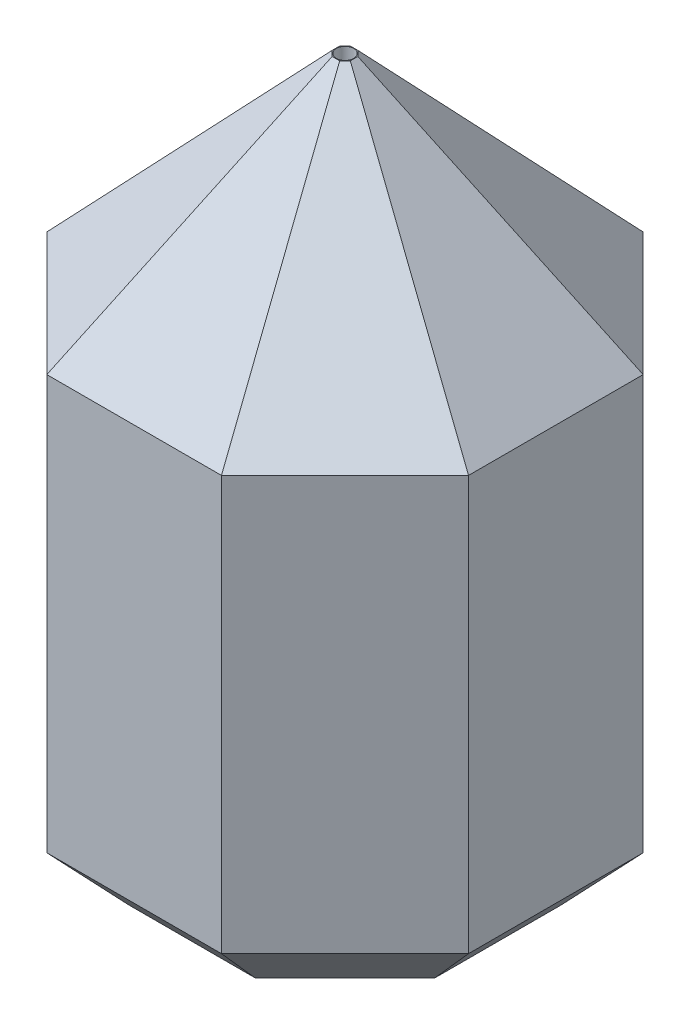
SolidWorks part; units mm, degrees
ref_plane "Front Plane" through (0, 0, 0) normal (0, 0, 1) x (1, 0, 0)
ref_plane "Top Plane" through (0, 0, 0) normal (0, 1, 0) x (1, 0, 0)
ref_plane "Right Plane" through (0, 0, 0) normal (1, 0, 0) x (0, 0, -1)
sketch "Sketch1" plane through (0, 0, 0) normal (0, 1, 0) x (1, 0, 0)
  line L1 (-17, -17) -> (17, -17)
  line L2 (-17, -17) -> (-17, 17)
  line L3 (-17, 17) -> (17, 17)
  line L4 (17, -17) -> (17, 17)
  line L5 (-17, -17) -> (17, 17) construction
  line L6 (-17, 17) -> (17, -17) construction
  line L7 (-15.136, 36.5416) -> (-36.5416, 15.136)
  line L8 (-36.5416, 15.136) -> (-36.5416, -15.136)
  line L9 (-36.5416, -15.136) -> (-15.136, -36.5416)
  line L10 (-15.136, -36.5416) -> (15.136, -36.5416)
  line L11 (15.136, -36.5416) -> (36.5416, -15.136)
  line L12 (36.5416, -15.136) -> (36.5416, 15.136)
  line L13 (36.5416, 15.136) -> (15.136, 36.5416)
  line L14 (15.136, 36.5416) -> (-15.136, 36.5416)
  circle A0 centre (0, 0) radius 36.5416 construction
  point P0 (0, 0)
  dimension "D1" = 34
  dimension "D2" = 34
  dimension "D3" = 12.5
extrude "Boss-Extrude1" add sketch "Sketch1" along normal blind 120
sketch "Sketch2" plane through (0, 120, 0) normal (0, 1, 0) x (1, 0, 0)
  line L8 (15.136, 36.5416) -> (-15.136, 36.5416)
  line L9 (-15.136, 36.5416) -> (-36.5416, 15.136)
  line L10 (-36.5416, 15.136) -> (-36.5416, -15.136)
  line L11 (-36.5416, -15.136) -> (-15.136, -36.5416)
  line L12 (-15.136, -36.5416) -> (15.136, -36.5416)
  line L13 (15.136, -36.5416) -> (36.5416, -15.136)
  line L14 (36.5416, -15.136) -> (36.5416, 15.136)
  line L15 (36.5416, 15.136) -> (15.136, 36.5416)
  line L16 (15.136, 36.5416) -> (-15.136, 36.5416)
  line L17 (-15.136, 36.5416) -> (-36.5416, 15.136)
  line L18 (-36.5416, 15.136) -> (-36.5416, -15.136)
  line L19 (-36.5416, -15.136) -> (-15.136, -36.5416)
  line L20 (-15.136, -36.5416) -> (15.136, -36.5416)
  line L21 (15.136, -36.5416) -> (36.5416, -15.136)
  line L22 (36.5416, -15.136) -> (36.5416, 15.136)
  line L23 (36.5416, 15.136) -> (15.136, 36.5416)
  circle A0 centre (0, 0) radius 1.5
  line M9 (15.136, 36.5416) -> (-15.136, 36.5416)
  line M10 (-15.136, 36.5416) -> (-36.5416, 15.136)
  line M11 (-36.5416, 15.136) -> (-36.5416, -15.136)
  line M12 (-36.5416, -15.136) -> (-15.136, -36.5416)
  line M13 (-15.136, -36.5416) -> (15.136, -36.5416)
  line M14 (15.136, -36.5416) -> (36.5416, -15.136)
  line M15 (36.5416, -15.136) -> (36.5416, 15.136)
  line M16 (36.5416, 15.136) -> (15.136, 36.5416)
  line M17 (-17, 17) -> (17, 17)
  line M18 (17, 17) -> (17, -17)
  line M19 (17, -17) -> (-17, -17)
  line M20 (-17, -17) -> (-17, 17)
  dimension "D1" = 3
  dimension "D2" = 0
extrude "Boss-Extrude2" add sketch "Sketch2" against normal blind 20 contours M16 M9 M10 M11 M12 M13 M14 M15 M20 M17 M18 M19 | A0 M17 M20 M19 M18
sketch "Sketch4" plane through (0, 100, 0) normal (0, -1, 0) x (1, 0, 0)
  line L4 (17, -17) -> (17, 17)
  line L5 (17, 17) -> (-17, 17)
  line L6 (-17, 17) -> (-17, -17)
  line L7 (-17, -17) -> (17, -17)
  line L12 (17, -17) -> (17, 17)
  line L13 (17, 17) -> (-17, 17)
  line L14 (-17, 17) -> (-17, -17)
  line L15 (-17, -17) -> (17, -17)
  circle A3 centre (0, 0) radius 1.5 construction
  circle A4 centre (0, 0) radius 1.5
  dimension "D1" = 0
extrude "Boss-Extrude5" add sketch "Sketch4" along normal blind 15
sketch "Sketch3" plane through (0, 85, 0) normal (0, -1, 0) x (1, 0, 0)
  line L4 (-17, -17) -> (17, -17)
  line L5 (17, -17) -> (17, 17)
  line L6 (17, 17) -> (-17, 17)
  line L7 (-17, 17) -> (-17, -17)
  line L12 (-17, -17) -> (17, -17)
  line L13 (17, -17) -> (17, 17)
  line L14 (17, 17) -> (-17, 17)
  line L15 (-17, 17) -> (-17, -17)
  circle A0 centre (0, 0) radius 8
  dimension "D2" = 16
  dimension "D1" = 0
extrude "Boss-Extrude3" add sketch "Sketch3" along normal blind 13
chamfer "Chamfer1" distance 37.5 angle 43 8 edges at (0, 120, -36.5416) (-25.8388, 120, -25.8388) (-36.5416, 120, 0) (-25.8388, 120, 25.8388) (25.8388, 120, -25.8388) (36.5416, 120, 0) (25.8388, 120, 25.8388) (0, 120, 36.5416)
chamfer "Chamfer2" distance 10 angle 47 8 edges at (-25.8388, 0, 25.8388) (-36.5416, 0, 0) (-25.8388, 0, -25.8388) (0, 0, -36.5416) (25.8388, 0, -25.8388) (36.5416, 0, 0) (25.8388, 0, 25.8388) (0, 0, 36.5416)
sketch "Sketch5" plane through (0, 0, 0) normal (0, -1, 0) x (1, 0, 0)
  line L0 (-17, -17) -> (-17, 17) construction
  line L1 (-17, -17) -> (-17, 17)
  line L3 (-12, -2) -> (-22, -2)
  line L4 (-12, -2) -> (-12, 2)
  line L5 (-12, 2) -> (-22, 2)
  line L6 (-22, -2) -> (-22, 2)
  line L7 (-12, -2) -> (-22, 2) construction
  line L8 (-12, 2) -> (-22, -2) construction
  point P2 (-17, 0)
  dimension "D1" = 4
  dimension "D2" = 5
extrude "Cut-Extrude1" cut sketch "Sketch5" against normal blind 20 contours L6 L3 L1 L5
